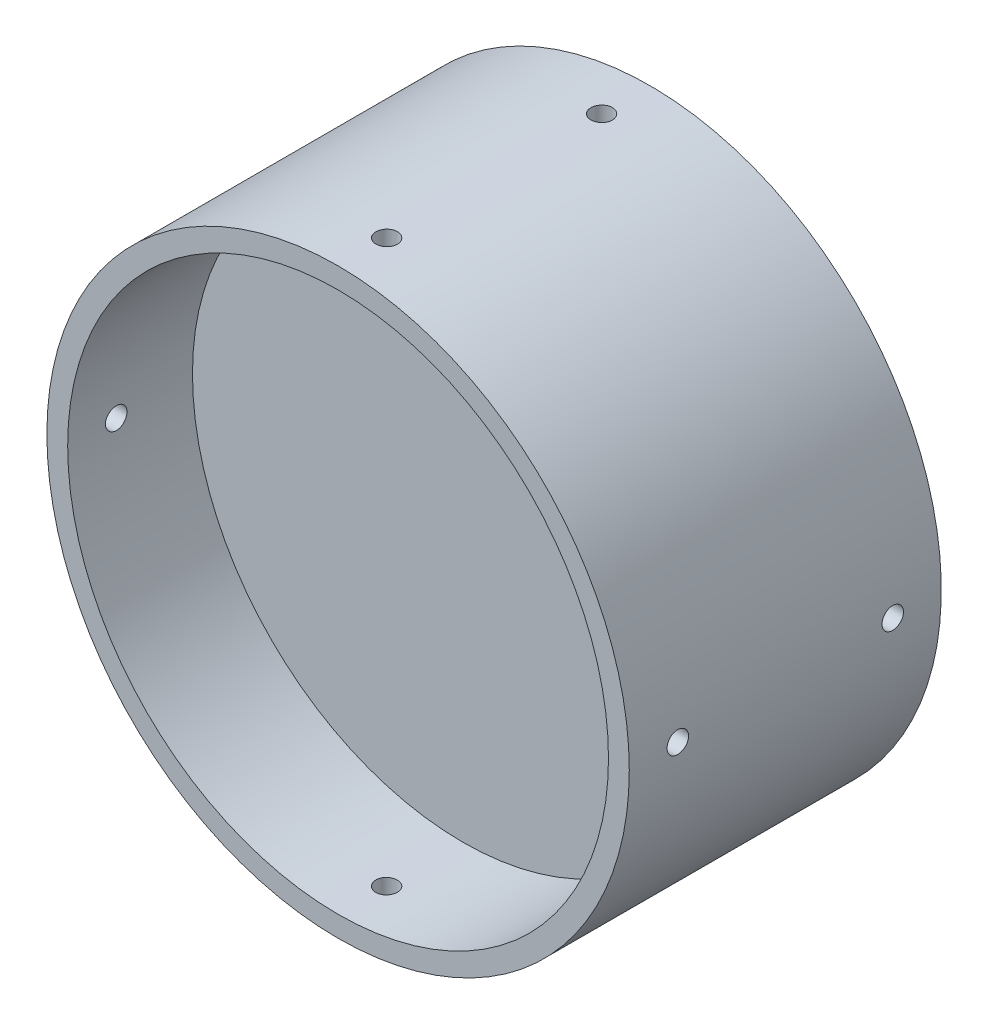
SolidWorks part; units mm, degrees
material "Alliage 1060"
ref_plane "Plan de face" through (0, 0, 0) normal (0, 0, 1) x (1, 0, 0)
ref_plane "Plan de dessus" through (0, 0, 0) normal (0, 1, 0) x (1, 0, 0)
ref_plane "Plan de droite" through (0, 0, 0) normal (1, 0, 0) x (0, 0, -1)
sketch "Esquisse1" plane through (0, 0, 0) normal (0, 0, 1) x (1, 0, 0)
  circle A0 centre (0, 0) radius 42
  dimension "D1" = 84
extrude "Boss.-Extru.1" add sketch "Esquisse1" along normal blind 33
hole_wizard "Trou taraudé M21" positions "Esquisse2" profile "Esquisse3" tap size "M2" standard "ISO"
sketch "Esquisse2" plane through (0, 0, 0) normal (0, 0, -1) x (-1, 0, 0)
  line L2 (0, 0) -> (47.1724, 47.1724) construction
  line L3 (0, 0) -> (0, 0.985) construction
  line L5 (0, 0) -> (0, 69.8377) construction
  point P0 (26.163, 26.163)
  dimension "D1" = 45
  dimension "D2" = 37
sketch "Esquisse3" plane through (-26.163, 26.163, 0) normal (1, 0, 0) x (0, 1, 0)
  line L0 (0, 0) -> (0, 6.4807)
  line L1 (0, 6.4807) -> (0.8, 6)
  line L2 (0.8, 6) -> (0.8, 0)
  line L5 (0.8, 0) -> (0, 0)
  line L10 (0, 6.4807) -> (-0.8, 6) construction
  line L11 (0, -6.35) -> (0, 107.95) construction
  dimension "Diamètre du trou pour taraudage" = 1.6
  dimension "Profondeur du trou pour taraudage" = 6
  dimension "Angle de pointe" = 118
cosmetic thread "Filetage de perçage1" parameters "D1"=4, "D2"=2
pattern_circular "Répétition circulaire1" count 4 over 360 about axis through (0, 0, 0) along (0, 0, 1) of "Trou taraudé M21"
sketch "Esquisse4" plane through (0, 0, 0) normal (0, 0, -1) x (-1, 0, 0)
sketch "Esquisse5" plane through (0, 0, 0) normal (0, 0, -1) x (-1, 0, 0)
  circle A0 centre (0, 0) radius 35
  dimension "D1" = 70
extrude "Enlèv. mat.-Extru.1" cut sketch "Esquisse5" against normal blind 13
sketch "Esquisse7" plane through (0, 0, 33) normal (0, 0, 1) x (1, 0, 0)
  circle A0 centre (0, 0) radius 39
  dimension "D1" = 78
extrude "Enlèv. mat.-Extru.2" cut sketch "Esquisse7" against normal blind 18
sketch "Esquisse9" plane through (0, 0, 33) normal (0, 0, 1) x (1, 0, 0)
  line L0 (0, 0) -> (0, 59.152) construction
  line L1 (-23.5999, 54.0878) -> (-22.0338, 53.198) construction
  line L3 (0.8391, 39.8781) -> (-0.8467, 40.8359) construction
hole_wizard "Dégagement M2.51" positions "Esquisse3D2" profile "Esquisse13" hole size "M2.5" standard "ISO"
sketch3d "Esquisse3D2"
  line L0 (42, 0, 0) -> (42, 0, 33) construction
  line L3 (0, 0, 33) -> (92.9027, 0, 33) construction
  circle A0 centre (0, 0, 33) radius 42 construction
  point P14 (0, 0, 75)
  point P18 (42, 0, 26)
  dimension "D1" = 7
sketch "Esquisse13" plane through (42, 0, 26) normal (0, 1, 0) x (0, 0, -1)
  line L0 (0, 0) -> (0, 10.9313)
  line L1 (0, 10.9313) -> (1.55, 10)
  line L2 (1.55, 10) -> (1.55, 0)
  line L5 (1.55, 0) -> (0, 0)
  line L10 (0, 10.9313) -> (-1.55, 10) construction
  line L11 (0, -6.35) -> (0, 107.95) construction
  dimension "Diamètre du perçage" = 3.1
  dimension "Profondeur du perçage" = 10
  dimension "Angle de pointe" = 118
pattern_circular "Répétition circulaire2" count 4 over 360 about axis through (0, 0, 33) along (0, 0, 1) of "Dégagement M2.51"
sketch "Esquisse14" plane through (0, 0, 0) normal (0, 1, 0) x (1, 0, 0)
  line L0 (42, 0) -> (42, 12)
  line L1 (42, 12) -> (39, 12)
  line L2 (39, 12) -> (39, 0)
  line L3 (39, 0) -> (42, 0)
  line L4 (0, 20.1232) -> (0, -43.3354) construction
  dimension "D1" = 3
  dimension "D2" = 12
revolve "Révolution1" add sketch "Esquisse14" angle 360 about L4
hole_wizard "Dégagement M2.52" positions "Esquisse3D3" profile "Esquisse15" hole size "M2.5" standard "ISO"
sketch3d "Esquisse3D3"
  line L2 (42, 0, 38.8023) -> (42, 0, -12) construction
  line L3 (0, 0, -12) -> (64.394, 0, -12) construction
  line L4 (0, 0, 33) -> (0, 0, -12) construction
  point P0 (42, 0, -5)
  dimension "D1" = 7
sketch "Esquisse15" plane through (42, 0, -5) normal (0, 1, 0) x (0, 0, -1)
  line L0 (0, 0) -> (0, 9.4313)
  line L1 (0, 9.4313) -> (1.55, 8.5)
  line L2 (1.55, 8.5) -> (1.55, 0)
  line L5 (1.55, 0) -> (0, 0)
  line L10 (0, 9.4313) -> (-1.55, 8.5) construction
  line L11 (0, -6.35) -> (0, 107.95) construction
  dimension "Diamètre du perçage" = 3.1
  dimension "Profondeur du perçage" = 8.5
  dimension "Angle de pointe" = 118
pattern_circular "Répétition circulaire3" count 4 over 360 of "Dégagement M2.52"
